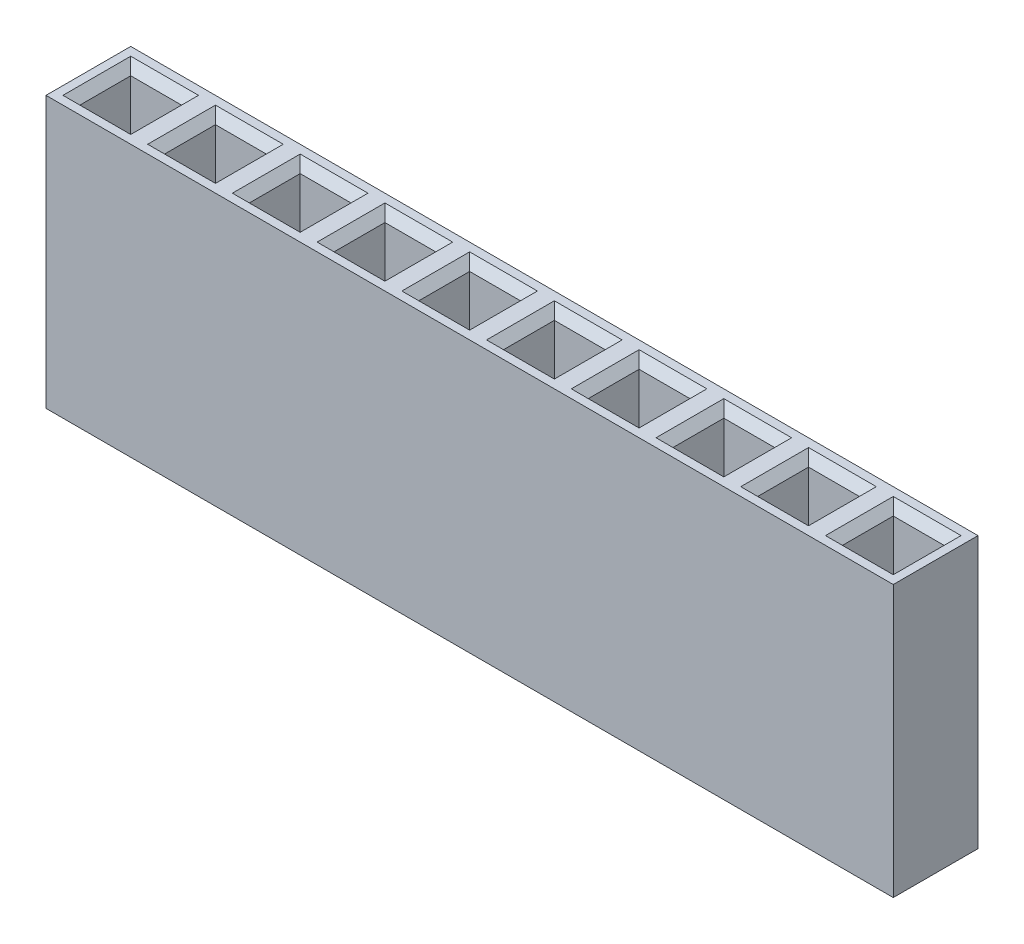
SolidWorks part; units mm, degrees
ref_plane "Front Plane" through (0, 0, 0) normal (0, 0, 1) x (1, 0, 0)
ref_plane "Top Plane" through (0, 0, 0) normal (0, 1, 0) x (1, 0, 0)
ref_plane "Right Plane" through (0, 0, 0) normal (1, 0, 0) x (0, 0, -1)
sketch "Sketch1" plane through (0, 0, 0) normal (0, 0, 1) x (1, 0, 0)
  line L1 (-1.25, -4) -> (1.25, -4)
  line L2 (-1.25, -4) -> (-1.25, 4)
  line L3 (-1.25, 4) -> (1.25, 4)
  line L4 (1.25, -4) -> (1.25, 4)
  line L5 (-1.25, -4) -> (1.25, 4) construction
  line L6 (-1.25, 4) -> (1.25, -4) construction
  point P0 (0, 0)
  dimension "D1" = 8
  dimension "D2" = 2.5
extrude "Boss-Extrude1" add sketch "Sketch1" along normal blind 2.5
sketch "Sketch2" plane through (0, 4, 0) normal (0, 1, 0) x (1, 0, 0)
  line L0 (0.75, -0.5) -> (-0.75, -0.5)
  line L1 (-0.75, -0.5) -> (-0.75, -2)
  line L2 (-0.75, -2) -> (0.75, -2)
  line L3 (0.75, -2) -> (0.75, -0.5)
  line L4 (1.25, 0) -> (-1.25, 0)
  line L5 (-1.25, 0) -> (-1.25, -2.5)
  line L6 (-1.25, -2.5) -> (1.25, -2.5)
  line L7 (1.25, -2.5) -> (1.25, 0)
  line L8 (1.25, 0) -> (-1.25, 0)
  line L9 (-1.25, 0) -> (-1.25, -2.5)
  line L10 (-1.25, -2.5) -> (1.25, -2.5)
  line L11 (1.25, -2.5) -> (1.25, 0)
  dimension "D1" = 0
  dimension "D2" = 0.5
extrude "Cut-Extrude2" cut sketch "Sketch2" against normal blind 7 contours L2 L3 L0 L1
chamfer "Chamfer3" distance 0.25 angle 45 4 edges at (0.75, 4, 1.25) (0, 4, 2) (-0.75, 4, 1.25) (0, 4, 0.5)
pattern_linear "LPattern2" count 10 spacing 2.5 along (1, 0, 0) of "Boss-Extrude1", "Cut-Extrude2", "Chamfer3"
